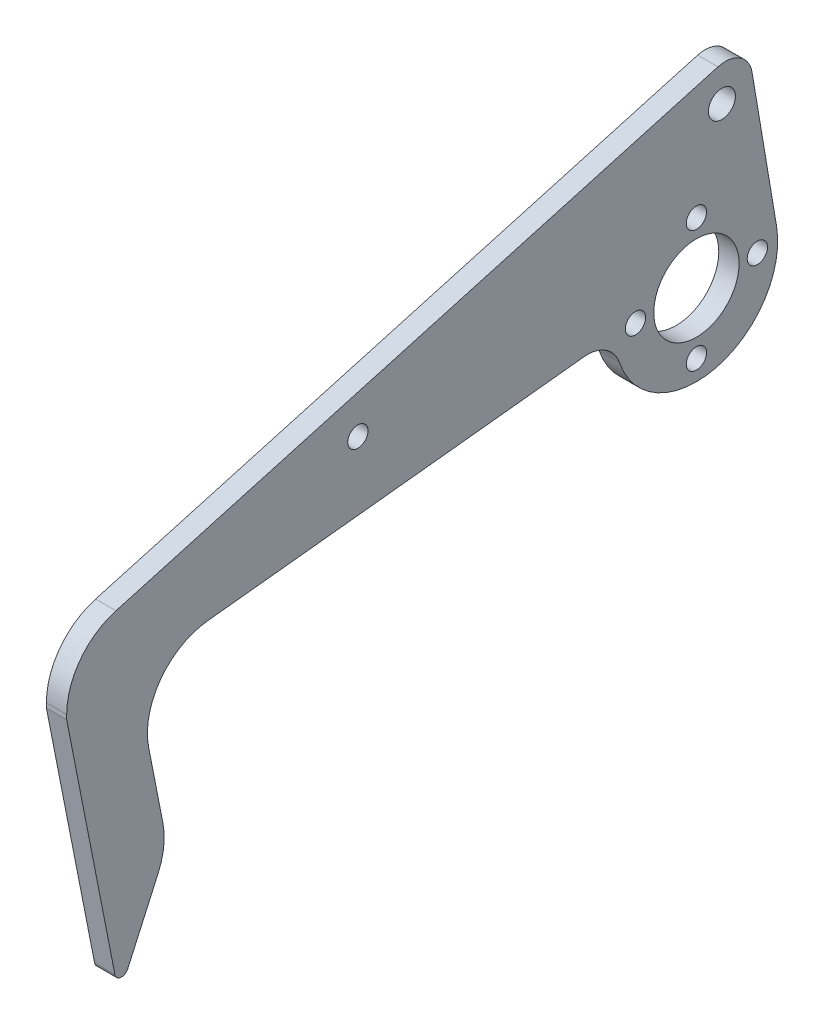
SolidWorks part; units mm, degrees
material "Thornel Mat VMA"
ref_plane "前视基准面" through (0, 0, 0) normal (0, 0, 1) x (1, 0, 0)
ref_plane "上视基准面" through (0, 0, 0) normal (0, 1, 0) x (1, 0, 0)
ref_plane "右视基准面" through (0, 0, 0) normal (1, 0, 0) x (0, 0, -1)
sketch "草图1" plane through (0, 0, 0) normal (1, 0, 0) x (0, 0, -1)
  circle A0 centre (0, 0) radius 9 construction
  circle A1 centre (0, 9) radius 1.5
  circle A2 centre (0, 0) radius 6.3
  circle A3 centre (0, 0) radius 12
  circle A4 centre (9, 0) radius 1.5
  circle A5 centre (0, -9) radius 1.5
  circle A6 centre (-9, 0) radius 1.5
  point P16 (0, 0)
  dimension "D1" = 12.6
  dimension "D2" = 3
  dimension "D3" = 18
  dimension "D4" = 24
  dimension "D5" = 4
extrude "凸台-拉伸1" add sketch "草图1" along normal blind 3
sketch "草图3" plane through (0, 0, 0) normal (-1, 0, 0) x (0, 0, 1)
  circle A0 centre (50, 6) radius 1.5
  dimension "D1" = 3
  dimension "D2" = 6
  dimension "D3" = 50
sketch "草图4" plane through (0, 0, 0) normal (-1, 0, 0) x (0, 0, 1)
  line L0 (78, 46.7243) -> (78, -60.4623) construction
  line L1 (20, -15) -> (40, -15) construction
  line L2 (20, -15) -> (20, -35) construction
  line L3 (20, -35) -> (40, -35) construction
  line L4 (40, -15) -> (40, -35) construction
  line L5 (43, -15) -> (63, -15) construction
  line L6 (43, -15) -> (43, -35) construction
  line L7 (43, -35) -> (63, -35) construction
  line L8 (63, -15) -> (63, -35) construction
  line L9 (43, -15) -> (63, -35) construction
  line L10 (63, -35) -> (63, -15) construction
  line L11 (63, -15) -> (43, -35) construction
  line L12 (8.4705, -8.5) -> (85.9497, -8.5) construction
  line L13 (0, 0) -> (5.2422, 0) construction
  line L14 (0, 0) -> (0, -4.4366) construction
  line L17 (78, -30) -> (78, 3)
  line L18 (78, 3) -> (18.9115, 13.4189)
  line L19 (18.9115, 13.4189) -> (-0.8775, 11.9679)
  line L21 (8.4705, -8.5) -> (67.3396, -4.5715)
  line L23 (67.3396, -4.5715) -> (68.5048, -22.0326)
  line L24 (68.5048, -22.0326) -> (78, -30)
  line L25 (11.3137, -4) -> (67.8353, -12)
  circle A1 centre (0, 0) radius 12 construction
  circle A2 centre (0, 0) radius 12 construction
  arc A3 (8.4705, -8.5) -> (-0.8775, 11.9679) centre (0, 0) ccw
  circle M7 centre (0, 0) radius 12
  dimension "D9" = 17.5
  dimension "D18" = 5
  dimension "D1" = 20
  dimension "D2" = 20
  dimension "D3" = 15
  dimension "D4" = 20
  dimension "D5" = 20
  dimension "D6" = 20
  dimension "D7" = 3
  dimension "D8" = 78
  dimension "D10" = 6.5
  dimension "D11" = 12
  dimension "D12" = 4
  dimension "D13" = 90
  dimension "D15" = 33
  dimension "D16" = 100
  dimension "D17" = 60
  dimension "D19" = 59
  dimension "D20" = 130
extrude "凸台-拉伸2" add sketch "草图4" against normal blind 3 contours L25 L21 L23 L24 L17 L18 L19 M7 | L21 L25 L23
fillet "圆角2" radius 30 1 edges at (1.5, 13.4189, 18.9115)
fillet "圆角4" radius 1 1 edges at (1.5, -30, 78)
extrude "切除-拉伸1" cut sketch "草图3" against normal blind 3
fillet "圆角6" radius 3 1 edges at (1.5, -22.0326, 68.5048)
sketch "草图5" plane through (3, 0, 0) normal (1, 0, 0) x (0, 0, -1)
  line L0 (0, 0) -> (-50, 6) construction
  line L1 (0, 0) -> (3.7761, 21.7644) construction
  line L2 (11.8336, 1.9914) -> (8.2121, 23.5116)
  line L5 (2.3413, 26.3534) -> (-22.2824, 12.8229)
  line L7 (11.8336, 1.9914) -> (0.8775, 11.9679)
  line L8 (0.8775, 11.9679) -> (-22.2824, 12.8229)
  circle A0 centre (3.7608, 21.6762) radius 2
  circle A1 centre (0, 0) radius 12 construction
  arc A2 (-15.1865, 13.1458) -> (-22.5898, 12.7703) centre (-17.3804, -16.7739) ccw construction
  arc A3 (8.2121, 23.5116) -> (2.3413, 26.3534) centre (4.2676, 22.8478) ccw
  dimension "D2" = 4
  dimension "D4" = 4
  dimension "D1" = 93
  dimension "D3" = 22
extrude "凸台-拉伸3" add sketch "草图5" against normal blind 3
fillet "圆角8" radius 3 1 edges at (1.5, 12.8229, 22.2824)
sketch "草图6" plane through (3, 0, 0) normal (1, 0, 0) x (0, 0, -1)
  line L0 (0, 27.5849) -> (0, -27.5849) construction
  line L1 (-12, 0) -> (-67.8353, -6)
  line L2 (-67.8353, -6) -> (-67.8353, -12)
  line L3 (-67.8353, -12) -> (-11.3137, -4)
  line L9 (-16.0317, -21.6098) -> (-17.9196, -1.6991)
  line L10 (-17.9196, -1.6991) -> (-37.8303, -3.5871)
  line L11 (-37.8303, -3.5871) -> (-35.9424, -23.4978)
  line L12 (-35.9424, -23.4978) -> (-16.0317, -21.6098)
  circle A0 centre (0, 0) radius 12
  arc A1 (-11.3137, -4) -> (11.8336, 1.9914) centre (0, 0) ccw construction
  point P5 (0, 0)
  line M13 (-67.8353, -12) -> (-11.3137, -4)
  dimension "D2" = 6
extrude "切除-拉伸2" cut sketch "草图6" against normal blind 10 contours A0 L1 L2 L11 L10 L3 M13 | L10 L11 L3
sketch "草图7" plane through (3, 0, 0) normal (1, 0, 0) x (0, 0, -1)
  line L0 (-78, -27.8555) -> (-78, -39.2077)
  line L1 (-78, -39.2077) -> (-65.6985, -28.8855)
  line L3 (-69.4847, -22.8548) -> (-76.3572, -28.6215) construction
  line L5 (-67.8353, -9) -> (-65.6985, -28.8855)
  line L6 (-67.8353, -6) -> (-67.8353, -12) construction
  line L8 (-12, 0) -> (-67.8353, -6) construction
  line L9 (-67.8353, -12) -> (-78, -27.8555)
  arc M8 (-78, -27.8555) -> (-76.3572, -28.6215) centre (-77, -27.8555) ccw
  line M9 (-76.3572, -28.6215) -> (-69.4847, -22.8548)
  arc M10 (-69.4847, -22.8548) -> (-68.4197, -20.7564) centre (-71.413, -20.5566) ccw
  line M11 (-68.4197, -20.7564) -> (-67.8353, -12)
  line M28 (-67.8353, -12) -> (-67.8353, -6)
  dimension "D1" = 90
  dimension "D2" = 20
extrude "凸台-拉伸4" add sketch "草图7" against normal up to surface (3 mm away) contours L5 L0 L1 M28 M11 M10 M9 M8 up to face at (0, 6, 51.5)
sketch "草图9" plane through (3, 0, 0) normal (1, 0, 0) x (0, 0, -1)
  line L0 (-51.4779, -4.2423) -> (-102.7307, -9.7498)
  line L1 (-102.7307, -9.7498) -> (-98.9335, -45.0859)
  line L2 (-98.9335, -45.0859) -> (-47.6807, -39.5783)
  line L3 (-47.6807, -39.5783) -> (-51.4779, -4.2423)
  line L4 (-12, 0) -> (-67.8353, -6) construction
extrude "切除-拉伸4" cut sketch "草图9" against normal through all
sketch "草图10" plane through (0, 0, 0) normal (-1, 0, 0) x (0, 0, 1)
  line L0 (78, -7.0923) -> (93, -8.7042)
  line L1 (93, -8.7042) -> (93, 0.3551)
  line L2 (93, 0.3551) -> (78, 3)
  line L3 (78, 3) -> (78, -7.0923)
  line L4 (78, 3) -> (22.7668, 12.7391) construction
  line L5 (12, 0) -> (78, -7.0923) construction
  dimension "D1" = 15
extrude "凸台-拉伸5" add sketch "草图10" against normal up to surface (3 mm away) up to face at (3, 7.7614, 23.5492)
sketch "草图11" plane through (0, 0, 0) normal (-1, 0, 0) x (0, 0, 1)
  line L0 (93, -8.7042) -> (85.2762, -47.9514)
  line L2 (78.1726, -32.1591) -> (83, -7.6296)
  line L3 (12, 0) -> (93, -8.7042) construction
  line L4 (83, -7.6296) -> (93, -8.7042)
  line L5 (85.2762, -47.9514) -> (78.1726, -32.1591)
  dimension "D1" = 10
  dimension "D2" = 40
  dimension "D3" = 85
  dimension "D4" = 25
extrude "凸台-拉伸6" add sketch "草图11" against normal up to surface (3 mm away) up to face at (3, 7.2293, 27.2992)
fillet "圆角9" radius 10 3 edges at (1.5, -32.1591, 78.1726) (1.5, 0.3551, 93) (1.5, -7.6296, 83)
fillet "圆角10" radius 1 1 edges at (1.5, -47.9514, 85.2762)
sketch "草图12" plane through (3, 0, 0) normal (1, 0, 0) x (0, 0, -1)
  line L0 (-85.7182, 1.5876) -> (3.1803, 26.6972)
  line L9 (-93, -8.7042) -> (-85.8822, -44.8725)
  line L10 (-83.989, -45.0896) -> (-79.48, -35.0654)
  line L11 (-78.788, -29.0322) -> (-80.8927, -18.3373)
  line L12 (-72.1494, -6.4636) -> (-12, 0)
  line L13 (11.8336, 1.9914) -> (8.2121, 23.5116)
  line L14 (2.3413, 26.3534) -> (-21.843, 13.0643)
  line L15 (-22.7668, 12.7391) -> (-84.7365, 1.8122)
  line L16 (-93, -8.0359) -> (-93, -8.7042)
  line L17 (-93, -8.7042) -> (-85.8822, -44.8725)
  line L18 (-83.989, -45.0896) -> (-79.48, -35.0654)
  line L19 (-78.788, -29.0322) -> (-80.8927, -18.3373)
  line L20 (-72.1494, -6.4636) -> (-12, 0)
  line L21 (11.8336, 1.9914) -> (8.2121, 23.5116)
  line L22 (2.3413, 26.3534) -> (-21.843, 13.0643)
  line L23 (-22.7668, 12.7391) -> (-84.7365, 1.8122)
  line L24 (-93, -8.0359) -> (-93, -8.7042)
  arc A0 (-84.7365, 1.8122) -> (-93, -8.0359) centre (-83, -8.0359) ccw construction
  arc A1 (8.2121, 23.5116) -> (2.3413, 26.3534) centre (4.2676, 22.8478) ccw construction
  arc A10 (-85.8822, -44.8725) -> (-83.989, -45.0896) centre (-84.901, -44.6794) ccw
  arc A11 (-79.48, -35.0654) -> (-78.788, -29.0322) centre (-88.5998, -30.9632) ccw
  arc A12 (-72.1494, -6.4636) -> (-80.8927, -18.3373) centre (-71.0809, -16.4063) ccw
  arc A13 (-12, 0) -> (11.8336, 1.9914) centre (0, 0) ccw
  arc A14 (8.2121, 23.5116) -> (2.3413, 26.3534) centre (4.2676, 22.8478) ccw
  arc A15 (-22.7668, 12.7391) -> (-21.843, 13.0643) centre (-23.2878, 15.6935) ccw
  arc A17 (-84.7365, 1.8122) -> (-93, -8.0359) centre (-83, -8.0359) ccw
  arc A18 (-85.8822, -44.8725) -> (-83.989, -45.0896) centre (-84.901, -44.6794) ccw
  arc A19 (-79.48, -35.0654) -> (-78.788, -29.0322) centre (-88.5998, -30.9632) ccw
  arc A20 (-72.1494, -6.4636) -> (-80.8927, -18.3373) centre (-71.0809, -16.4063) ccw
  arc A21 (-12, 0) -> (11.8336, 1.9914) centre (0, 0) ccw
  arc A22 (8.2121, 23.5116) -> (2.3413, 26.3534) centre (4.2676, 22.8478) ccw
  arc A23 (-22.7668, 12.7391) -> (-21.843, 13.0643) centre (-23.2878, 15.6935) ccw
  arc A25 (-84.7365, 1.8122) -> (-93, -8.0359) centre (-83, -8.0359) ccw
  dimension "D1" = 0
extrude "凸台-拉伸8" add sketch "草图12" against normal up to surface (3 mm away) up to face at (0, -8.3282, 52.5551)
fillet "圆角11" radius 5 1 edges at (1.5, 0, 12)
